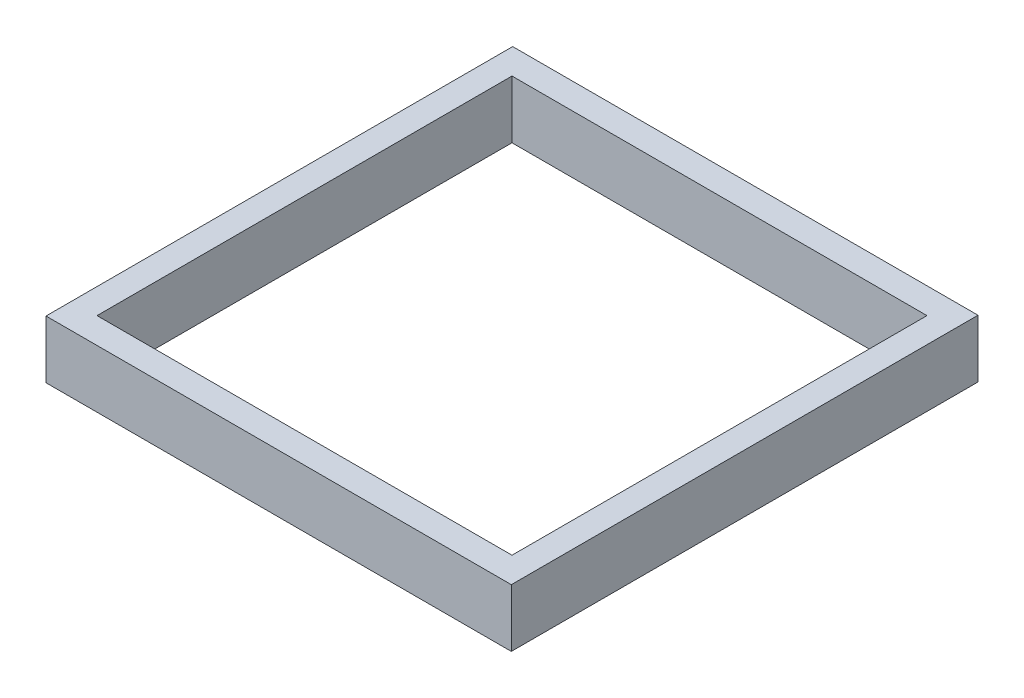
SolidWorks part; units mm, degrees
material "Plain Carbon Steel"
ref_plane "Front Plane" through (0, 0, 0) normal (0, 0, 1) x (1, 0, 0)
ref_plane "Top Plane" through (0, 0, 0) normal (0, 1, 0) x (1, 0, 0)
ref_plane "Right Plane" through (0, 0, 0) normal (1, 0, 0) x (0, 0, -1)
sketch "Sketch1" plane through (0, 0, 0) normal (0, 0, 1) x (1, 0, 0)
  line L1 (0, 0) -> (37, 0)
  line L2 (0, 0) -> (0, 85)
  line L3 (0, 85) -> (37, 85)
  line L4 (37, 0) -> (37, 85)
  line L5 (-610, 0) -> (-647, 0)
  line L6 (-610, 0) -> (-610, 85)
  line L7 (-610, 85) -> (-647, 85)
  line L8 (-647, 0) -> (-647, 85)
  dimension "D1" = 37
  dimension "D2" = 85
  dimension "D3" = 85
  dimension "D4" = 37
  dimension "D5" = 610
extrude "Boss-Extrude1" add sketch "Sketch1" along normal blind 686
sketch "Sketch2" plane through (-610, 0, 0) normal (1, 0, 0) x (0, 0, -1)
  line L0 (-686, 85) -> (0, 85) construction
  line L1 (-686, 0) -> (-648, 0)
  line L2 (-686, 0) -> (-686, 85)
  line L3 (-686, 85) -> (-648, 85)
  line L4 (-648, 0) -> (-648, 85)
  line L6 (0, 0) -> (-38, 0)
  line L7 (0, 0) -> (0, 85)
  line L8 (0, 85) -> (-38, 85)
  line L9 (-38, 0) -> (-38, 85)
  dimension "D1" = 38
  dimension "D2" = 38
extrude "Boss-Extrude2" add sketch "Sketch2" along normal blind 610
